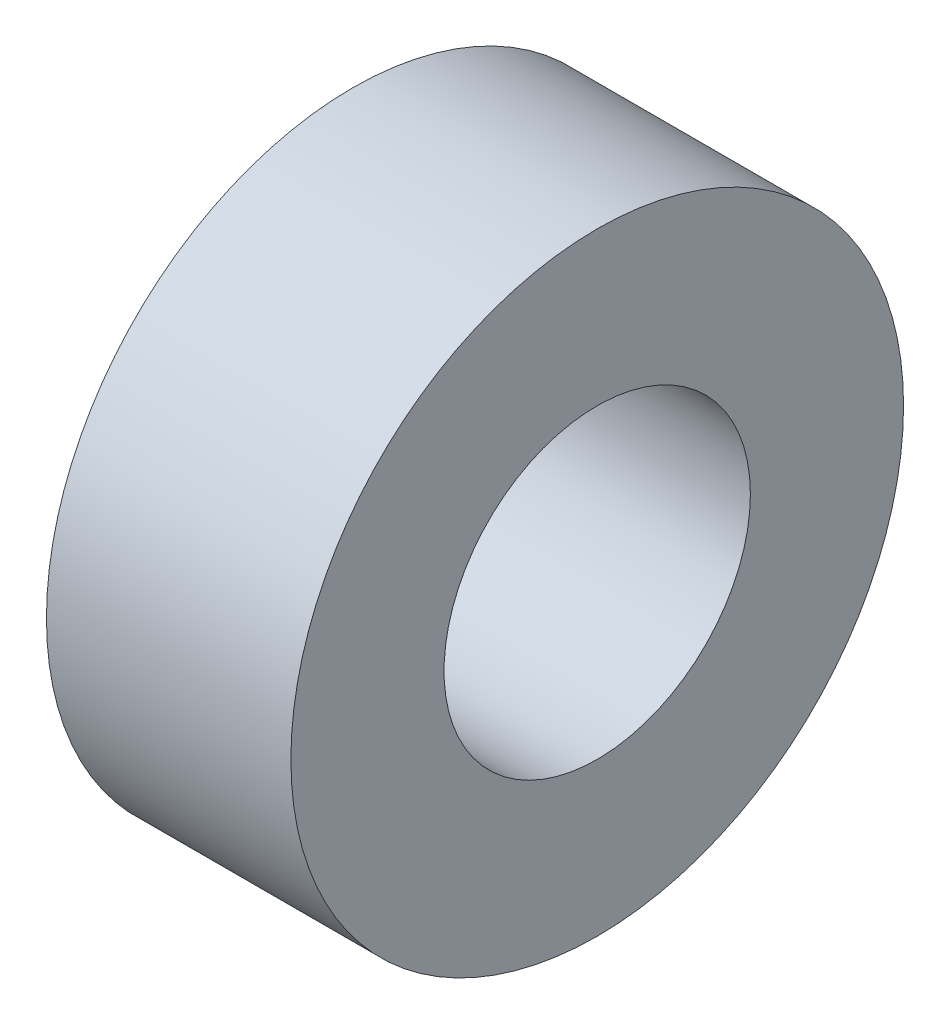
SolidWorks part; units mm, degrees
material "Nylon 101"
ref_plane "Front Plane" through (0, 0, 0) normal (0, 0, 1) x (1, 0, 0)
ref_plane "Top Plane" through (0, 0, 0) normal (0, 1, 0) x (1, 0, 0)
ref_plane "Right Plane" through (0, 0, 0) normal (1, 0, 0) x (0, 0, -1)
sketch "Sketch1" plane through (0, 0, 0) normal (1, 0, 0) x (0, 0, -1)
  circle A0 centre (0, 0) radius 9.525
  circle A1 centre (0, 0) radius 4.7625
  dimension "D1" = 9.525
  dimension "D2" = 19.05
extrude "Boss-Extrude1" add sketch "Sketch1" along normal blind 7.6004
